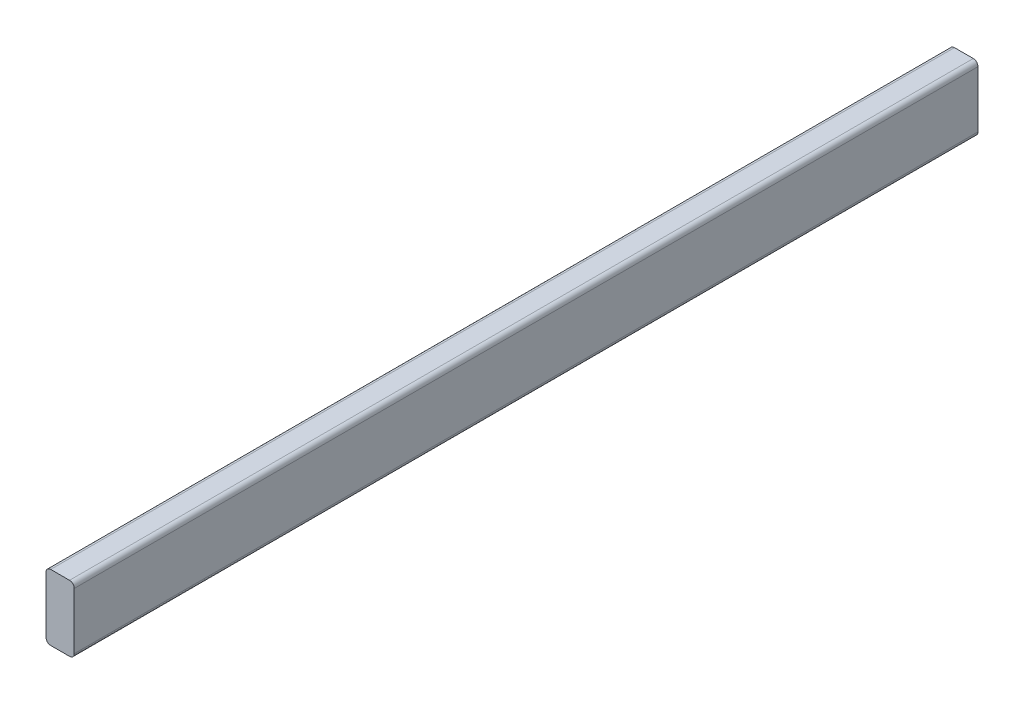
SolidWorks part; units mm, degrees
material "Oak"
ref_plane "Front Plane" through (0, 0, 0) normal (0, 0, 1) x (1, 0, 0)
ref_plane "Top Plane" through (0, 0, 0) normal (0, 1, 0) x (1, 0, 0)
ref_plane "Right Plane" through (0, 0, 0) normal (1, 0, 0) x (0, 0, -1)
sketch "Sketch2" plane through (0, 0, 0) normal (0, 0, 1) x (1, 0, 0)
  line L1 (-12.7, 44.45) -> (12.7, 44.45)
  line L2 (-19.05, 38.1) -> (-19.05, -38.1)
  line L3 (-12.7, -44.45) -> (12.7, -44.45)
  line L4 (19.05, 38.1) -> (19.05, -38.1)
  line L5 (-19.05, 44.45) -> (19.05, -44.45) construction
  line L6 (-19.05, -44.45) -> (19.05, 44.45) construction
  arc A0 (-19.05, -38.1) -> (-12.7, -44.45) centre (-12.7, -38.1) ccw
  arc A1 (12.7, -44.45) -> (19.05, -38.1) centre (12.7, -38.1) ccw
  arc A2 (12.7, 44.45) -> (19.05, 38.1) centre (12.7, 38.1) cw
  arc A3 (-12.7, 44.45) -> (-19.05, 38.1) centre (-12.7, 38.1) ccw
  point P0 (0, 0)
  dimension "D3" = 6.35
  dimension "D1" = 88.9
  dimension "D2" = 38.1
extrude "Boss-Extrude1" add sketch "Sketch2" along normal blind 1219.2
